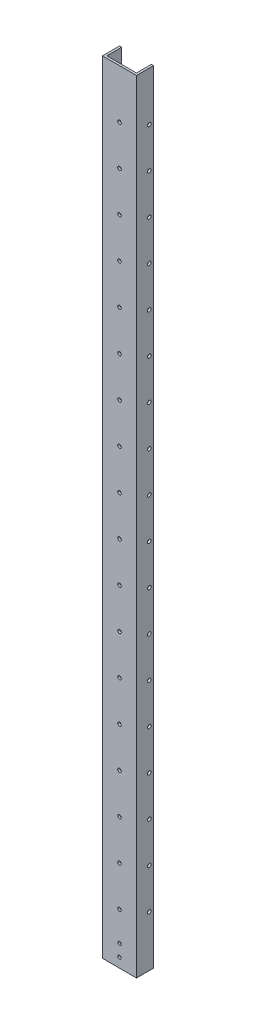
SolidWorks part; units mm, degrees
ref_plane "Front" through (0, 0, 0) normal (0, 0, 1) x (1, 0, 0)
ref_plane "Top" through (0, 0, 0) normal (0, 1, 0) x (1, 0, 0)
ref_plane "Right" through (0, 0, 0) normal (1, 0, 0) x (0, 0, -1)
sketch "Sketch1" plane through (0, 0, 0) normal (0, 1, 0) x (1, 0, 0)
  line L0 (3.175, 3.175) -> (3.175, 25.4)
  line L1 (0, 0) -> (50.8, 0)
  line L2 (0, 0) -> (0, 25.4)
  line L4 (50.8, 0) -> (50.8, 25.4)
  line L5 (3.175, 3.175) -> (47.625, 3.175)
  line L6 (47.625, 3.175) -> (47.625, 25.4)
  line L7 (0, 25.4) -> (3.175, 25.4)
  line L8 (50.8, 25.4) -> (47.625, 25.4)
  dimension "D1" = 25.4
  dimension "D2" = 50.8
  dimension "D3" = 3.175
extrude "Boss-Extrude1" add sketch "Sketch1" along normal blind 1168.4
sketch "Sketch2" plane through (0, 0, 0) normal (0, 0, 1) x (1, 0, 0)
  line L0 (25.4, 0) -> (25.4, 76.2) construction
  line L1 (0, 0) -> (50.8, 0) construction
  circle A0 centre (25.4, 76.2) radius 2.667
  circle A1 centre (25.4, 136.144) radius 2.667
  circle A2 centre (25.4, 196.088) radius 2.667
  circle A3 centre (25.4, 256.032) radius 2.667
  circle A4 centre (25.4, 315.976) radius 2.667
  circle A5 centre (25.4, 375.92) radius 2.667
  circle A6 centre (25.4, 435.864) radius 2.667
  circle A7 centre (25.4, 495.808) radius 2.667
  circle A8 centre (25.4, 555.752) radius 2.667
  circle A9 centre (25.4, 615.696) radius 2.667
  circle A10 centre (25.4, 675.64) radius 2.667
  circle A11 centre (25.4, 735.584) radius 2.667
  circle A12 centre (25.4, 795.528) radius 2.667
  circle A13 centre (25.4, 855.472) radius 2.667
  circle A14 centre (25.4, 915.416) radius 2.667
  circle A15 centre (25.4, 975.36) radius 2.667
  circle A16 centre (25.4, 1035.304) radius 2.667
  circle A17 centre (25.4, 1095.248) radius 2.667
  dimension "D2" = 5.334
  dimension "D1" = 76.2
  dimension "D3" = 18
extrude "Cut-Extrude1" cut sketch "Sketch2" against normal up to next
ref_plane "Mid_Plane" through (25.4, 0, 0) normal (1, 0, 0) x (0, 0, -1)
sketch "Sketch3" plane through (0, 0, 0) normal (0, 0, 1) x (1, 0, 0)
  circle A1 centre (25.4, 32.131) radius 2.5527
  circle A3 centre (25.4, 14.2875) radius 2.5527
extrude "Cut-Extrude2" cut sketch "Sketch3" against normal up to next
sketch "Sketch4" plane through (50.8, 0, 0) normal (-1, 0, 0) x (0, 0, 1)
  line L0 (-19.05, 76.2) -> (-19.05, 0) construction
  line L1 (-25.4, 0) -> (0, 0) construction
  line L2 (-19.05, 76.2) -> (-25.4, 76.2) construction
  line L3 (-25.4, 1168.4) -> (-25.4, 0) construction
  line L4 (-19.05, 76.2) -> (-19.05, 136.144) construction
  circle A0 centre (-19.05, 76.2) radius 2.667
  circle A1 centre (-19.05, 136.144) radius 2.667
  circle A2 centre (-19.05, 196.088) radius 2.667
  circle A3 centre (-19.05, 256.032) radius 2.667
  circle A4 centre (-19.05, 315.976) radius 2.667
  circle A5 centre (-19.05, 375.92) radius 2.667
  circle A6 centre (-19.05, 435.864) radius 2.667
  circle A7 centre (-19.05, 495.808) radius 2.667
  circle A8 centre (-19.05, 555.752) radius 2.667
  circle A9 centre (-19.05, 615.696) radius 2.667
  circle A10 centre (-19.05, 675.64) radius 2.667
  circle A11 centre (-19.05, 735.584) radius 2.667
  circle A12 centre (-19.05, 795.528) radius 2.667
  circle A13 centre (-19.05, 855.472) radius 2.667
  circle A14 centre (-19.05, 915.416) radius 2.667
  circle A15 centre (-19.05, 975.36) radius 2.667
  circle A16 centre (-19.05, 1035.304) radius 2.667
  circle A17 centre (-19.05, 1095.248) radius 2.667
  dimension "D1" = 5.334
  dimension "D2" = 6.35
  dimension "D3" = 76.2
  dimension "D5" = 59.944
  dimension "D4" = 18
extrude "Cut-Extrude3" cut sketch "Sketch4" along normal up to next
